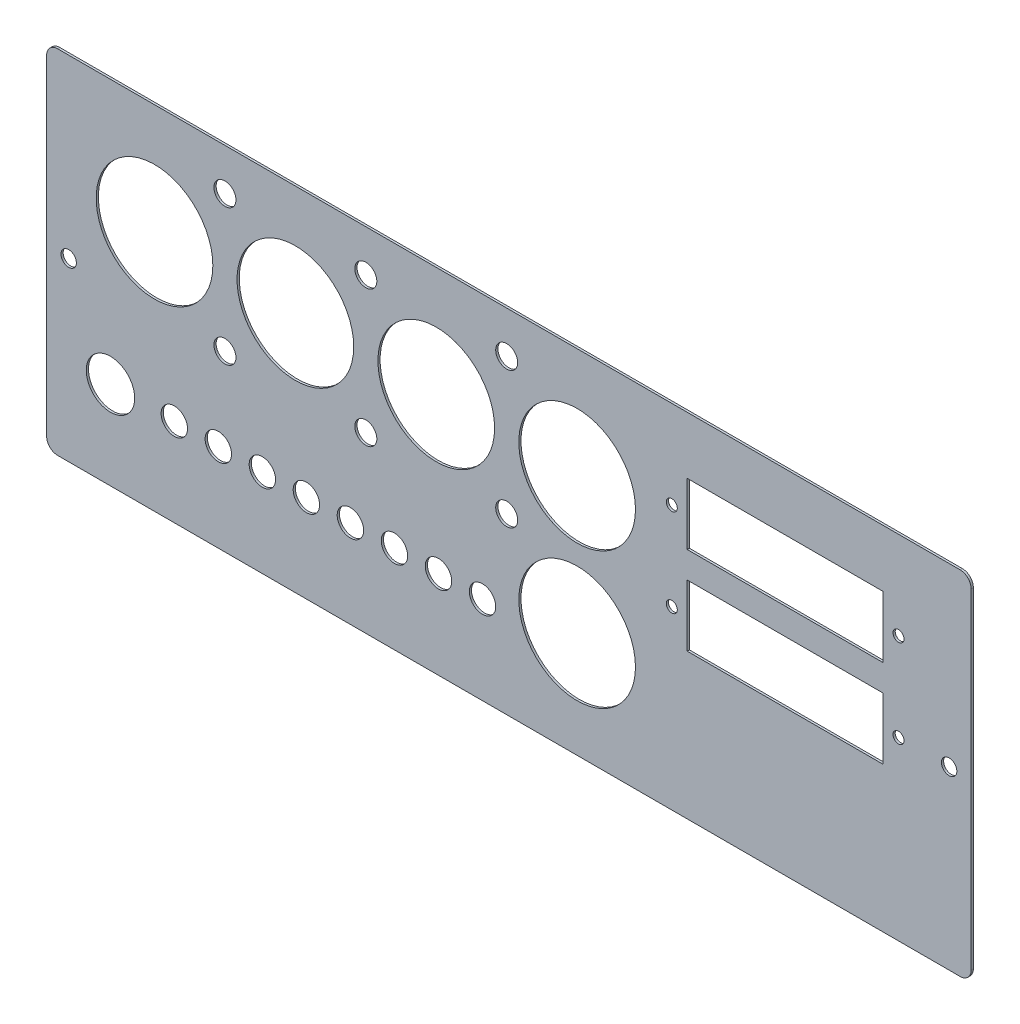
SolidWorks part; units mm, degrees
ref_plane "Plan de face" through (0, 0, 0) normal (0, 0, 1) x (1, 0, 0)
ref_plane "Plan de dessus" through (0, 0, 0) normal (0, 1, 0) x (1, 0, 0)
ref_plane "Plan de droite" through (0, 0, 0) normal (1, 0, 0) x (0, 0, -1)
sketch "Esquisse1" plane through (0, 0, 0) normal (0, 0, 1) x (1, 0, 0)
  line L0 (0, 80) -> (0, -80) construction
  line L1 (205, 80) -> (-205, 80)
  line L2 (210, 75) -> (210, -75)
  line L3 (205, -80) -> (-205, -80)
  line L4 (-210, 75) -> (-210, -75)
  line L5 (-161, 30) -> (-97, 30) construction
  line L6 (-97, 30) -> (-33, 30) construction
  line L7 (-33, 30) -> (31, 30) construction
  line L8 (74, 40) -> (81, 40) construction
  line L9 (81, 54) -> (170, 54)
  line L10 (81, 54) -> (81, 26)
  line L11 (81, 26) -> (170, 26)
  line L12 (170, 54) -> (170, 26)
  line L13 (125.5, 26) -> (125.5, 54) construction
  line L14 (81, 40) -> (170, 40) construction
  line L15 (81, 14) -> (170, 14)
  line L16 (81, 14) -> (81, -14)
  line L17 (81, -14) -> (170, -14)
  line L18 (170, 14) -> (170, -14)
  line L19 (125.5, -14) -> (125.5, 14) construction
  line L20 (81, 0) -> (170, 0) construction
  line L21 (81, 0) -> (74, 0) construction
  line L22 (170, 0) -> (177, 0) construction
  line L23 (170, 40) -> (177, 40) construction
  line L24 (31, 30) -> (31, -32) construction
  line L25 (-129, 61) -> (-129, -1) construction
  line L26 (-65, 61) -> (-65, -1) construction
  line L27 (-1, 61) -> (-1, -1) construction
  line L28 (-210, -40) -> (-181, -40) construction
  line L29 (-181, -40) -> (-152, -40) construction
  line L30 (-210, 0) -> (-200, 0) construction
  line L31 (200, 0) -> (210, 0) construction
  circle A0 centre (-161, 30) radius 26.5
  circle A1 centre (-97, 30) radius 26.5
  circle A2 centre (-33, 30) radius 26.5
  circle A3 centre (31, 30) radius 26.5
  circle A4 centre (74, 40) radius 2.5
  circle A5 centre (74, 0) radius 2.5
  circle A6 centre (177, 0) radius 2.5
  circle A7 centre (177, 40) radius 2.5
  circle A8 centre (31, -32) radius 26.5
  circle A9 centre (-129, 61) radius 5
  circle A10 centre (-65, 61) radius 5
  circle A11 centre (-1, 61) radius 5
  circle A12 centre (-1, -1) radius 5
  circle A13 centre (-65, -1) radius 5
  circle A14 centre (-129, -1) radius 5
  circle A15 centre (-181, -40) radius 11
  circle A16 centre (-152, -40) radius 6
  circle A17 centre (200, 0) radius 3.5
  circle A18 centre (-200, 0) radius 3.5
  circle A19 centre (-132, -40) radius 6
  circle A20 centre (-112, -40) radius 6
  circle A21 centre (-92, -40) radius 6
  circle A22 centre (-72, -40) radius 6
  circle A23 centre (-52, -40) radius 6
  circle A24 centre (-32, -40) radius 6
  circle A25 centre (-12, -40) radius 6
  arc A26 (205, 80) -> (210, 75) centre (205, 75) cw
  arc A27 (210, -75) -> (205, -80) centre (205, -75) cw
  arc A28 (-205, -80) -> (-210, -75) centre (-205, -75) cw
  arc A29 (-205, 80) -> (-210, 75) centre (-205, 75) ccw
  point P0 (0, 0)
  point P16 (125.5, 40)
  point P20 (125.5, 0)
  point P40 (-65, 30)
  point P41 (-1, 30)
  point P43 (-129, 30)
  point P54 (-187.5, 30)
  point P84 (210, 80)
  point P89 (-210, -80)
  point P92 (-210, 80)
  point P93 (57.5, 30)
  dimension "D3" = 53
  dimension "D4" = 22.5
  dimension "D5" = 50
  dimension "D13" = 5
  dimension "D15" = 10
  dimension "D18" = 22
  dimension "D20" = 7
  dimension "D22" = 12
  dimension "D26" = 5
  dimension "D1" = 160
  dimension "D2" = 420
  dimension "D6" = 64
  dimension "D7" = 89
  dimension "D8" = 28
  dimension "D9" = 12
  dimension "D10" = 26
  dimension "D11" = 40
  dimension "D12" = 103
  dimension "D14" = 62
  dimension "D16" = 62
  dimension "D17" = 29
  dimension "D19" = 40
  dimension "D21" = 10
  dimension "D24" = 20
  dimension "D25" = 66
  dimension "D27" = 19
  dimension "D28" = 50
  dimension "D23" = 8
extrude "Boss.-Extru.1" add sketch "Esquisse1" along normal blind 1
